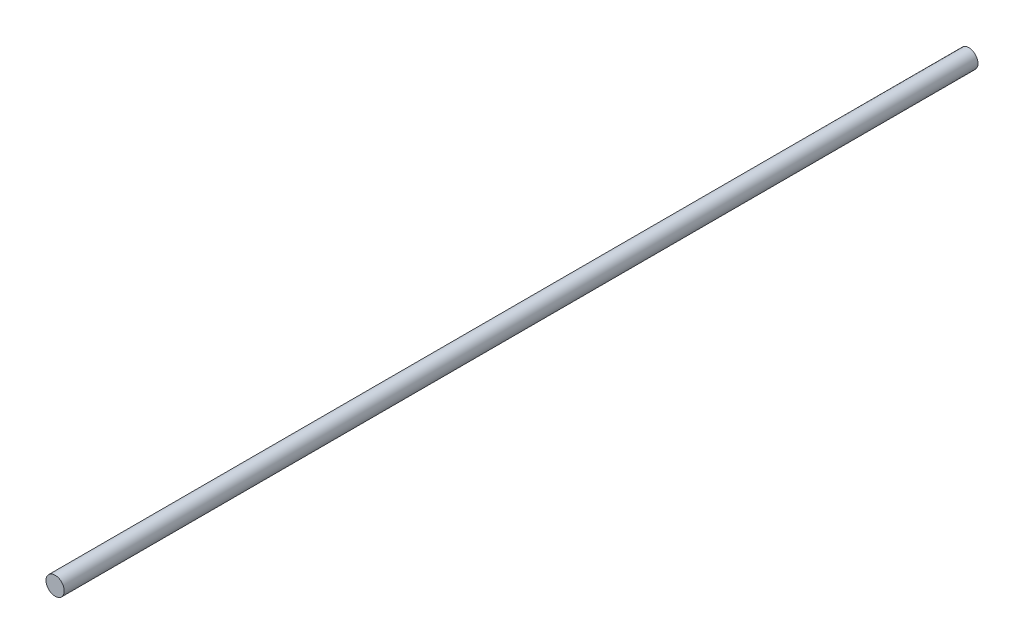
SolidWorks part; units mm, degrees
ref_plane "Front" through (0, 0, 0) normal (0, 0, 1) x (1, 0, 0)
ref_plane "Top" through (0, 0, 0) normal (0, 1, 0) x (1, 0, 0)
ref_plane "Right" through (0, 0, 0) normal (1, 0, 0) x (0, 0, -1)
sketch "Sketch1" plane through (0, 0, 0) normal (0, 0, 1) x (1, 0, 0)
  circle A0 centre (0, 0) radius 4
  dimension "D1" = 8
extrude "Boss-Extrude1" add sketch "Sketch1" along normal blind 400
